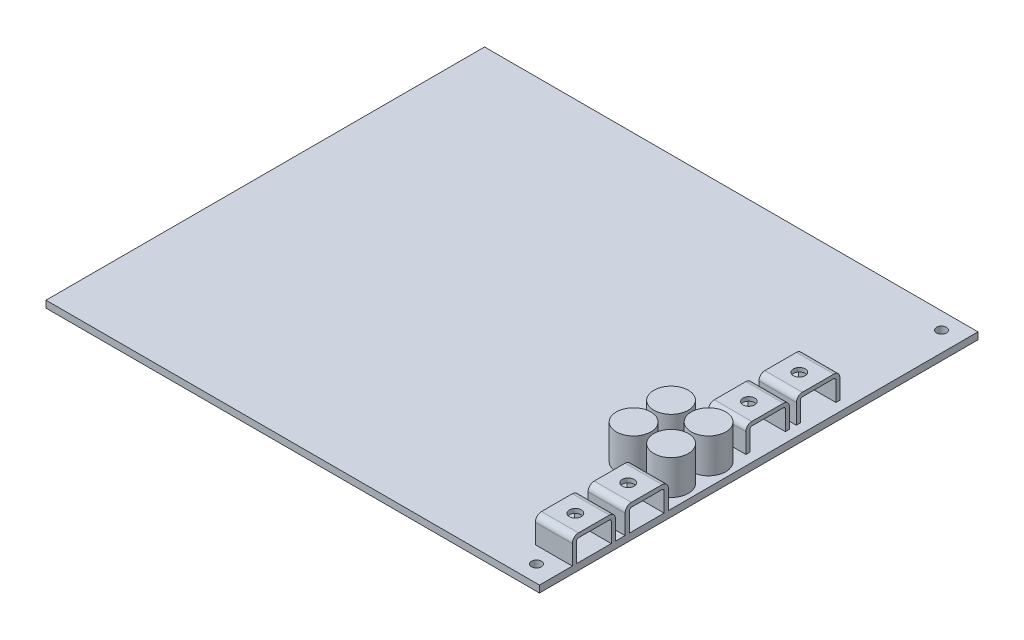
SolidWorks part; units mm, degrees
ref_plane "Front Plane" through (0, 0, 0) normal (0, 0, 1) x (1, 0, 0)
ref_plane "Top Plane" through (0, 0, 0) normal (0, 1, 0) x (1, 0, 0)
ref_plane "Right Plane" through (0, 0, 0) normal (1, 0, 0) x (0, 0, -1)
sketch "Sketch1" plane through (0, 0, 0) normal (0, 1, 0) x (1, 0, 0)
  line L1 (-63.5, -56.4388) -> (63.5, -56.4388)
  line L2 (-63.5, -56.4388) -> (-63.5, 56.4388)
  line L3 (-63.5, 56.4388) -> (63.5, 56.4388)
  line L4 (63.5, -56.4388) -> (63.5, 56.4388)
  line L5 (-63.5, -56.4388) -> (63.5, 56.4388) construction
  line L6 (-63.5, 56.4388) -> (63.5, -56.4388) construction
  point P0 (0, 0)
  dimension "D1" = 112.8776
  dimension "D2" = 127
extrude "Boss-Extrude1" add sketch "Sketch1" along normal blind 1.778
sketch "Sketch2" plane through (0, 1.778, 0) normal (0, 1, 0) x (1, 0, 0)
  line L0 (63.5, 56.4388) -> (-63.5, 56.4388) construction
  line L1 (63.5, -56.4388) -> (63.5, 56.4388) construction
  line L2 (-63.5, -56.4388) -> (63.5, -56.4388) construction
  circle A0 centre (58.42, 52.1208) radius 1.27
  circle A1 centre (58.42, -52.1208) radius 1.27
  dimension "D1" = 4.318
  dimension "D2" = 5.08
  dimension "D3" = 5.08
  dimension "D4" = 4.318
  dimension "D5" = 2.54
  dimension "D6" = 2.54
extrude "Cut-Extrude1" cut sketch "Sketch2" against normal up to surface (1.778 mm away) up to face at (0, 0, 0)
sketch "Sketch3" plane through (63.5, 0, 0) normal (1, 0, 0) x (0, 0, -1)
  line L0 (-56.4388, 1.778) -> (56.4388, 1.778) construction
  line L1 (-46.8884, 1.778) -> (-46.8884, 6.7818)
  line L2 (-47.9806, 1.778) -> (-47.9806, 6.7818)
  line L3 (-46.3804, 8.382) -> (-38.4556, 8.382)
  line L4 (-36.8554, 1.778) -> (-36.8554, 6.7818)
  line L5 (-56.4388, 1.778) -> (-56.4388, 0) construction
  line L6 (-46.3804, 7.2898) -> (-38.4556, 7.2898)
  line L7 (-37.9476, 1.778) -> (-37.9476, 6.7818)
  line L8 (-47.9806, 1.778) -> (-46.8884, 1.778)
  line L9 (-37.9476, 1.778) -> (-36.8554, 1.778)
  line L10 (-37.9476, 1.778) -> (-37.9476, 7.2898) construction
  line L11 (-46.8884, 7.2898) -> (-37.9476, 7.2898) construction
  line L12 (-46.8884, 1.778) -> (-46.8884, 7.2898) construction
  line L13 (-36.8554, 1.778) -> (-36.8554, 8.382) construction
  line L14 (-47.9806, 8.382) -> (-36.8554, 8.382) construction
  line L15 (-47.9806, 1.778) -> (-47.9806, 8.382) construction
  arc A0 (-37.9476, 6.7818) -> (-38.4556, 7.2898) centre (-38.4556, 6.7818) ccw
  arc A1 (-46.3804, 7.2898) -> (-46.8884, 6.7818) centre (-46.3804, 6.7818) ccw
  arc A2 (-36.8554, 6.7818) -> (-38.4556, 8.382) centre (-38.4556, 6.7818) ccw
  arc A3 (-46.3804, 8.382) -> (-47.9806, 6.7818) centre (-46.3804, 6.7818) ccw
  point P21 (-36.8554, 8.382)
  dimension "D4" = 0.508
  dimension "D5" = 1.6002
  dimension "D1" = 8.4582
extrude "Boss-Extrude2" add sketch "Sketch3" against normal blind 9.525
sketch "Sketch4" plane through (0, 8.382, 0) normal (0, 1, 0) x (1, 0, 0)
  circle A0 centre (58.7375, -42.418) radius 1.524
extrude "Cut-Extrude2" cut sketch "Sketch4" against normal up to surface (1.0922 mm away) up to face at (58.7375, 7.2898, 42.418)
pattern_linear "LPattern1" count 2 spacing 13.589 along (0, 0, -1) of "Cut-Extrude2", "Boss-Extrude2"
ref_plane "Plane1" through (60.96, 0, 0) normal (1, 0, 0) x (0, 0, -1)
sketch "Sketch5" plane through (60.96, 0, 0) normal (1, 0, 0) x (0, 0, -1)
  line L0 (23.4188, 1.778) -> (23.4188, 8.382)
  line L1 (56.4388, 1.778) -> (-56.4388, 1.778) construction
  line L2 (23.4188, 8.382) -> (12.2428, 8.382)
  line L3 (12.2428, 8.382) -> (12.2428, 1.778)
  line L4 (22.4028, 1.778) -> (22.4028, 7.366)
  line L5 (22.4028, 7.366) -> (13.2588, 7.366)
  line L6 (13.2588, 7.366) -> (13.2588, 1.778)
  line L7 (23.4188, 1.778) -> (22.4028, 1.778)
  line L8 (13.2588, 1.778) -> (12.2428, 1.778)
  line L9 (56.4388, 1.778) -> (56.4388, 0) construction
  dimension "D1" = 11.176
  dimension "D2" = 6.604
  dimension "D4" = 33.02
  dimension "D3" = 1.016
extrude "Boss-Extrude3" add sketch "Sketch5" against normal blind 9.652
sketch "Sketch6" plane through (0, 8.382, 0) normal (0, 1, 0) x (1, 0, 0)
  circle A0 centre (56.134, 17.8308) radius 1.524
extrude "Cut-Extrude3" cut sketch "Sketch6" against normal up to surface (1.016 mm away) up to face at (56.134, 7.366, -17.8308)
fillet "Fillet1" radius 1.524 2 edges at (56.134, 8.382, -12.2428) (56.134, 8.382, -23.4188)
fillet "Fillet2" radius 0.508 2 edges at (56.134, 7.366, -13.2588) (56.134, 7.366, -22.4028)
pattern_linear "LPattern2" count 2 spacing 13.0048 along (0, 0, 1) of "Boss-Extrude3"
sketch "Sketch7" plane through (0, 8.382, 0) normal (0, 1, 0) x (1, 0, 0)
  circle A0 centre (56.134, 4.826) radius 1.524
extrude "Cut-Extrude4" cut sketch "Sketch7" against normal up to surface (1.016 mm away) up to face at (56.134, 7.366, -4.826)
fillet "Fillet3" radius 0.508 2 edges at (56.134, 7.366, -9.398) (56.134, 7.366, -0.254)
fillet "Fillet4" radius 1.524 2 edges at (56.134, 8.382, -10.414) (56.134, 8.382, 0.762)
sketch "Sketch8" plane through (0, 1.778, 0) normal (0, 1, 0) x (1, 0, 0)
  line L0 (63.5, -23.2664) -> (63.5, 56.4388) construction
  line L3 (53.975, -23.2664) -> (63.5, -23.2664) construction
  circle A0 centre (57.785, -7.1882) radius 4.445
  circle A1 centre (57.785, -16.8402) radius 4.445
  circle A2 centre (48.133, -7.1882) radius 4.445
  circle A3 centre (48.133, -16.8402) radius 4.445
  dimension "D1" = 5.715
  dimension "D2" = 9.652
  dimension "D3" = 9.652
  dimension "D4" = 9.652
  dimension "D5" = 9.652
  dimension "D6" = 6.4262
extrude "Boss-Extrude4" add sketch "Sketch8" along normal blind 8.89
